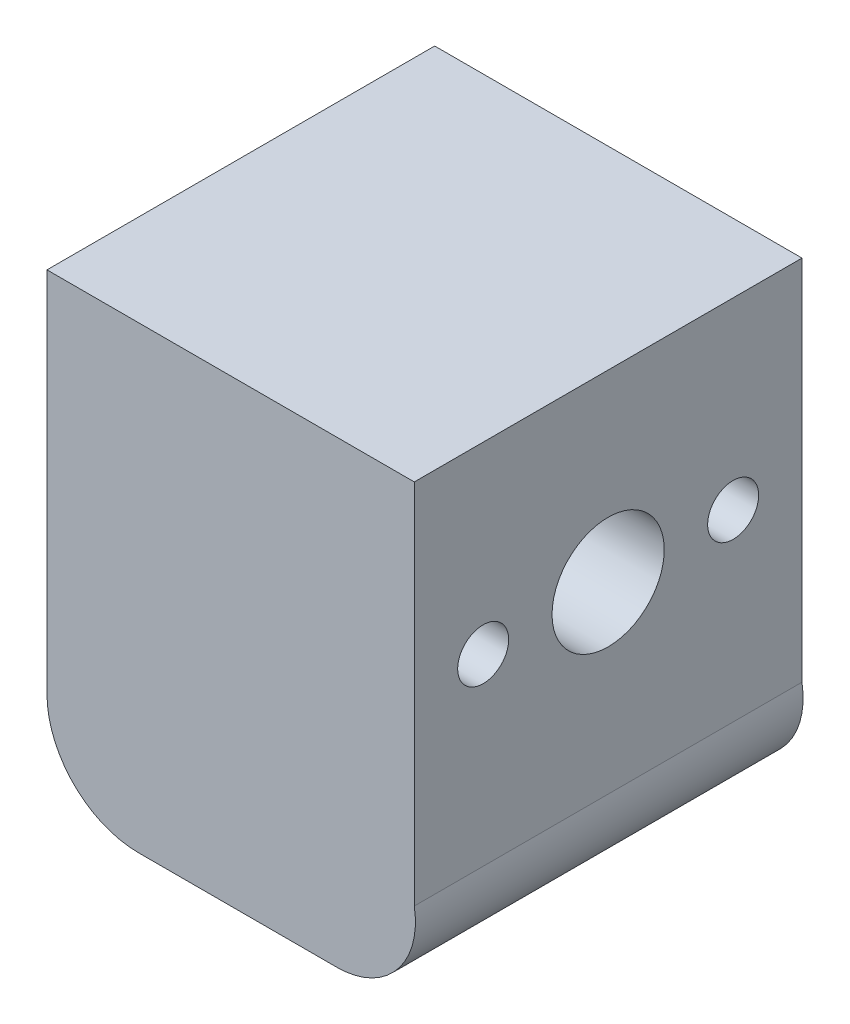
SolidWorks part; units mm, degrees
ref_plane "Front Plane" through (0, 0, 0) normal (0, 0, 1) x (1, 0, 0)
ref_plane "Top Plane" through (0, 0, 0) normal (0, 1, 0) x (1, 0, 0)
ref_plane "Right Plane" through (0, 0, 0) normal (1, 0, 0) x (0, 0, -1)
sketch "Sketch2" plane through (0, 0, 0) normal (0, 0, 1) x (1, 0, 0)
  line L0 (-37.2041, 20.6616) -> (-37.2041, 2.6616)
  line L2 (-32.7073, -1.8352) -> (-22.9997, -1.8352)
  line L3 (-19.2041, 2.6616) -> (-19.2041, 20.6616)
  line L5 (-19.2041, 20.6616) -> (-37.2041, 20.6616)
  arc A0 (-37.2041, 2.6616) -> (-32.7073, -1.8352) centre (-32.7073, 2.6616) ccw
  arc A2 (-22.9997, -1.8352) -> (-19.2041, 2.6616) centre (-22.9997, 2.0151) ccw
  point P0 (0, 0)
  dimension "D1" = 18
  dimension "D2" = 18
  dimension "D3" = 18
extrude "Boss-Extrude1" add sketch "Sketch2" along normal mid plane 19
sketch "Sketch3" plane through (-37.2041, 0, 0) normal (-1, 0, 0) x (0, 0, 1)
  line L0 (-9.5, 20.6616) -> (-9.5, 2.6616) construction
  line L3 (9.5, 20.6616) -> (9.5, 2.6616) construction
  circle A0 centre (0, 11.6616) radius 2.75
  circle A1 centre (6.125, 11.6616) radius 1.25
  circle A2 centre (-6.125, 11.6616) radius 1.25
  point P6 (0, 0)
  point P9 (-9.5, 11.6616)
  dimension "D1" = 2.5
  dimension "D2" = 2.5
  dimension "D3" = 5.5
  dimension "D4" = 3.375
  dimension "D5" = 9.5
  dimension "D6" = 3.375
extrude "Cut-Extrude1" cut sketch "Sketch3" against normal through all
